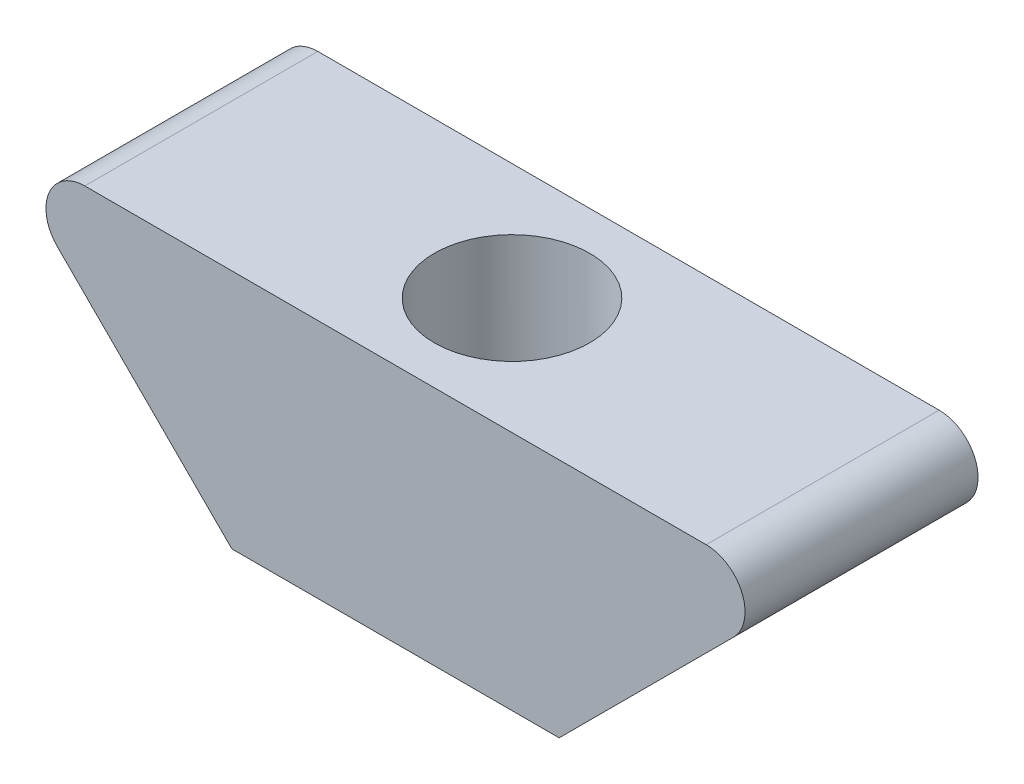
SolidWorks part; units mm, degrees
ref_plane "Front Plane" through (0, 0, 0) normal (0, 0, 1) x (1, 0, 0)
ref_plane "Top Plane" through (0, 0, 0) normal (0, 1, 0) x (1, 0, 0)
ref_plane "Right Plane" through (0, 0, 0) normal (1, 0, 0) x (0, 0, -1)
sketch "Sketch1" plane through (0, 0, 0) normal (0, 0, 1) x (1, 0, 0)
  line L0 (-8, 3.1) -> (8, 3.1)
  line L1 (8.7029, 1.3887) -> (4.2142, -3.1)
  line L2 (4.2142, -3.1) -> (-4.2142, -3.1)
  line L3 (0, 3.1) -> (0, -3.1) construction
  line L4 (-8.7029, 1.3887) -> (-4.2142, -3.1)
  arc A0 (8, 3.1) -> (8.7029, 1.3887) centre (8, 2.1) cw
  arc A1 (-8, 3.1) -> (-8.7029, 1.3887) centre (-8, 2.1) ccw
  dimension "D2" = 1
  dimension "D1" = 8
  dimension "D3" = 45
  dimension "D4" = 1.85
  dimension "D5" = 6.2
extrude "Boss-Extrude1" add sketch "Sketch1" along normal blind 6
sketch "Sketch2" plane through (0, 3.1, 0) normal (0, 1, 0) x (1, 0, 0)
  circle A0 centre (0, -3) radius 2
  dimension "D1" = 4
  dimension "D2" = 3
extrude "Cut-Extrude1" cut sketch "Sketch2" against normal blind 8
